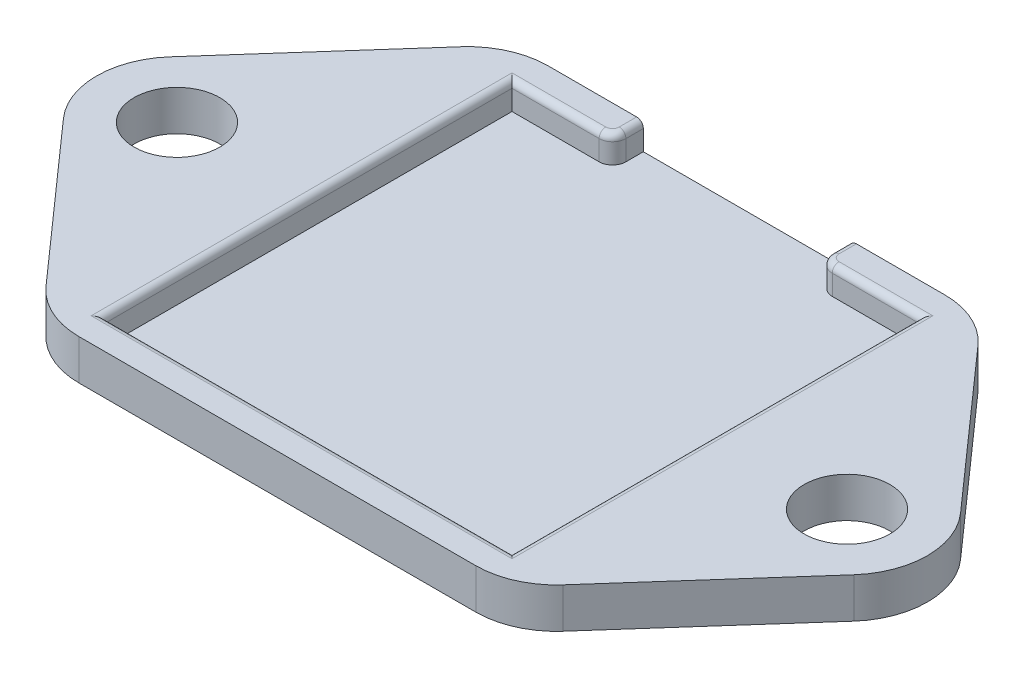
SolidWorks part; units mm, degrees
ref_plane "Front Plane" through (0, 0, 0) normal (0, 0, 1) x (1, 0, 0)
ref_plane "Top Plane" through (0, 0, 0) normal (0, 1, 0) x (1, 0, 0)
ref_plane "Right Plane" through (0, 0, 0) normal (1, 0, 0) x (0, 0, -1)
sketch "Sketch1" plane through (0, 0, 0) normal (0, 1, 0) x (1, 0, 0)
  line L0 (0, 0) -> (0, 17.5) construction
  line L1 (-17.5, -17.5) -> (17.5, -17.5)
  line L2 (-17.5, -17.5) -> (-17.5, 17.5) construction
  line L3 (-17.5, 17.5) -> (17.5, 17.5)
  line L4 (17.5, -17.5) -> (17.5, 17.5) construction
  line L5 (-17.5, -17.5) -> (17.5, 17.5) construction
  line L6 (-17.5, 17.5) -> (17.5, -17.5) construction
  line L7 (-17.5, 17.5) -> (-29.489, 3.981)
  line L8 (-29.489, -3.981) -> (-17.5, -17.5)
  line L9 (29.489, -3.981) -> (17.5, -17.5)
  line L10 (17.5, 17.5) -> (29.489, 3.981)
  circle A0 centre (-25, 0) radius 3.2
  arc A1 (-29.489, 3.981) -> (-29.489, -3.981) centre (-25, 0) ccw
  arc A2 (29.489, 3.981) -> (29.489, -3.981) centre (25, 0) cw
  circle A3 centre (25, 0) radius 3.2
  point P0 (0, 0)
  dimension "D2" = 50
  dimension "D3" = 6.4
  dimension "D4" = 6
  dimension "D1" = 35
extrude "Boss-Extrude1" add sketch "Sketch1" along normal blind 3
sketch "Sketch2" plane through (0, 3, 0) normal (0, 1, 0) x (1, 0, 0)
  line L0 (17.5, 17.5) -> (-17.5, 17.5) construction
  line L1 (-15.2, 15.2) -> (-7.7, 15.2)
  line L2 (-15.2, 15.2) -> (-15.2, -15.2)
  line L3 (-15.2, -15.2) -> (15.2, -15.2)
  line L4 (15.2, 15.2) -> (15.2, -15.2)
  line L5 (-15.2, 15.2) -> (15.2, -15.2) construction
  line L6 (-15.2, -15.2) -> (15.2, 15.2) construction
  line L8 (-7.7, 15.2) -> (-7.7, 17.5)
  line L9 (-7.7, 17.5) -> (7.7, 17.5)
  line L10 (7.7, 15.2) -> (7.7, 17.5)
  line L11 (7.7, 15.2) -> (15.2, 15.2)
  point P0 (0, 0)
  point P12 (0, 17.5)
  dimension "D1" = 30.4
  dimension "D2" = 15.4
extrude "Cut-Extrude1" cut sketch "Sketch2" against normal blind 2
fillet "Fillet1" radius 6 4 edges at (17.5, 1.5, -17.5) (17.5, 1.5, 17.5) (-17.5, 1.5, 17.5) (-17.5, 1.5, -17.5)
fillet "Fillet2" radius 1 2 edges at (7.7, 2, -15.2) (-7.7, 2, -15.2)
fillet "Fillet3" radius 0.5 9 edges at (-7.7, 3, -16.85) (-7.9929, 3, -15.4929) (7.7, 3, -16.85) (7.9929, 3, -15.4929) (-11.95, 3, -15.2) (11.95, 3, -15.2) (15.2, 3, 0) (0, 3, 15.2) (-15.2, 3, 0)
